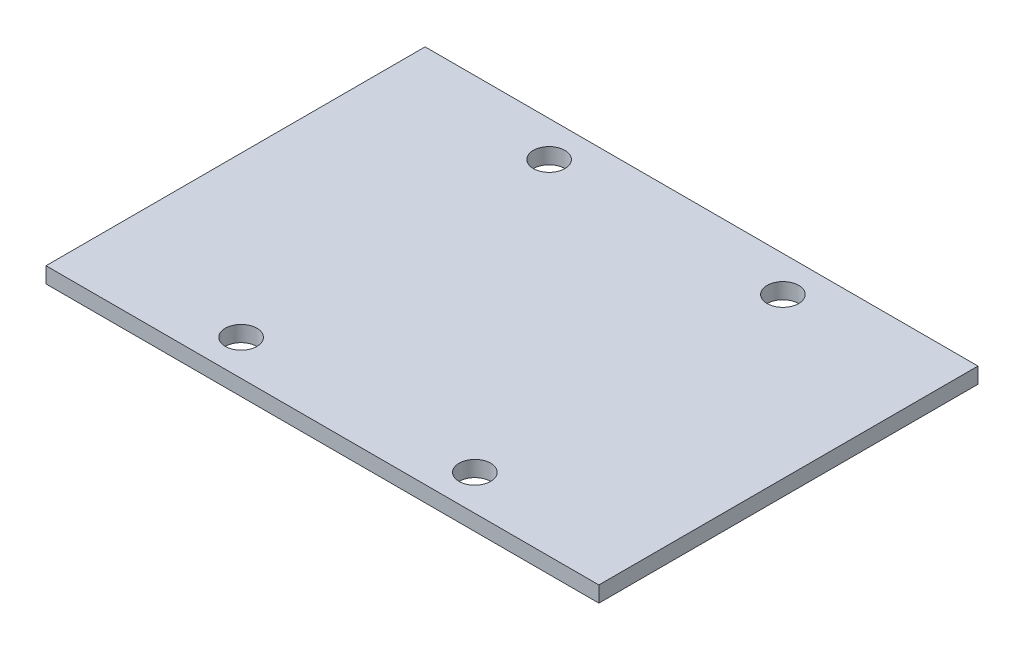
SolidWorks part; units mm, degrees
material "Hexcel AS4C (3000 丝)"
ref_plane "Front" through (0, 0, 0) normal (0, 0, 1) x (1, 0, 0)
ref_plane "Top" through (0, 0, 0) normal (0, 1, 0) x (1, 0, 0)
ref_plane "Right" through (0, 0, 0) normal (1, 0, 0) x (0, 0, -1)
sketch "草图1" plane through (0, 0, 0) normal (0, 1, 0) x (1, 0, 0)
  line L0 (0, 0) -> (20, 0) construction
  line L1 (0, 0) -> (0, -7.5) construction
  line L2 (0, -7.5) -> (-14.8, -7.5) construction
  line L4 (20, -12) -> (-20, -12)
  line L8 (0, 12) -> (20, 12) construction
  line L9 (20, 36) -> (-20, 36)
  line L12 (0, 0) -> (-35, 0) construction
  line L13 (-35, 0) -> (-35, 36) construction
  line L14 (-20, 36) -> (-35, 36)
  line L15 (-35, 36) -> (-35, -12)
  line L16 (-35, -12) -> (-20, -12)
  line L17 (35, -12) -> (20, -12)
  line L18 (20, 36) -> (35, 36)
  line L19 (35, 36) -> (35, -12)
  circle A0 centre (-14.8, -7.5) radius 2
  circle A1 centre (14.8, -7.5) radius 2
  circle A4 centre (14.8, 31.5) radius 2
  circle A5 centre (-14.8, 31.5) radius 2
  point P8 (20, 0)
  point P18 (0, -12)
  point P19 (0, 12)
  point P26 (-20, 12)
extrude "凸台-拉伸1" add sketch "草图1" along normal blind 2
